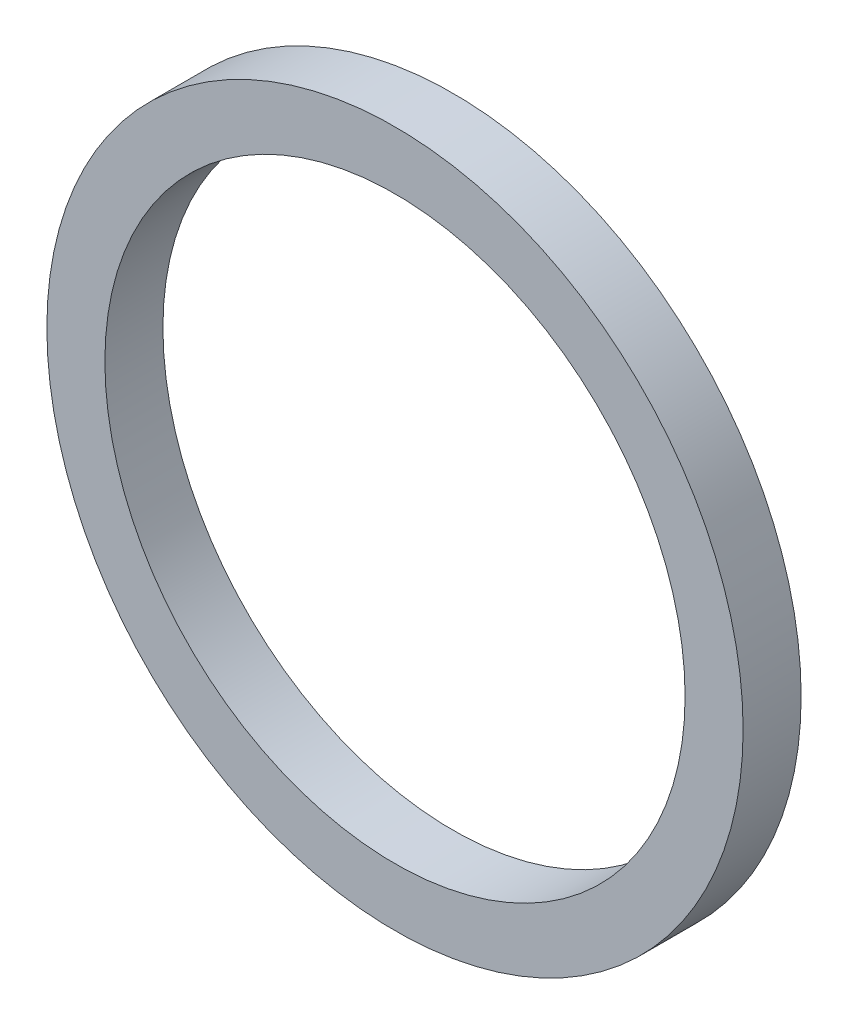
SolidWorks part; units mm, degrees
ref_plane "Front Plane" through (0, 0, 0) normal (0, 0, 1) x (1, 0, 0)
ref_plane "Top Plane" through (0, 0, 0) normal (0, 1, 0) x (1, 0, 0)
ref_plane "Right Plane" through (0, 0, 0) normal (1, 0, 0) x (0, 0, -1)
sketch "Sketch1" plane through (0, 0, 0) normal (0, 0, 1) x (1, 0, 0)
  circle A0 centre (0, 0) radius 15.24
  dimension "D1" = 30.48
extrude "Boss-Extrude1" add sketch "Sketch1" along normal blind 2.54
sketch "Sketch2" plane through (0, 0, 2.54) normal (0, 0, 1) x (1, 0, 0)
  circle A0 centre (0, 0) radius 12.7
  dimension "D1" = 25.4
extrude "Cut-Extrude1" cut sketch "Sketch2" against normal through all
